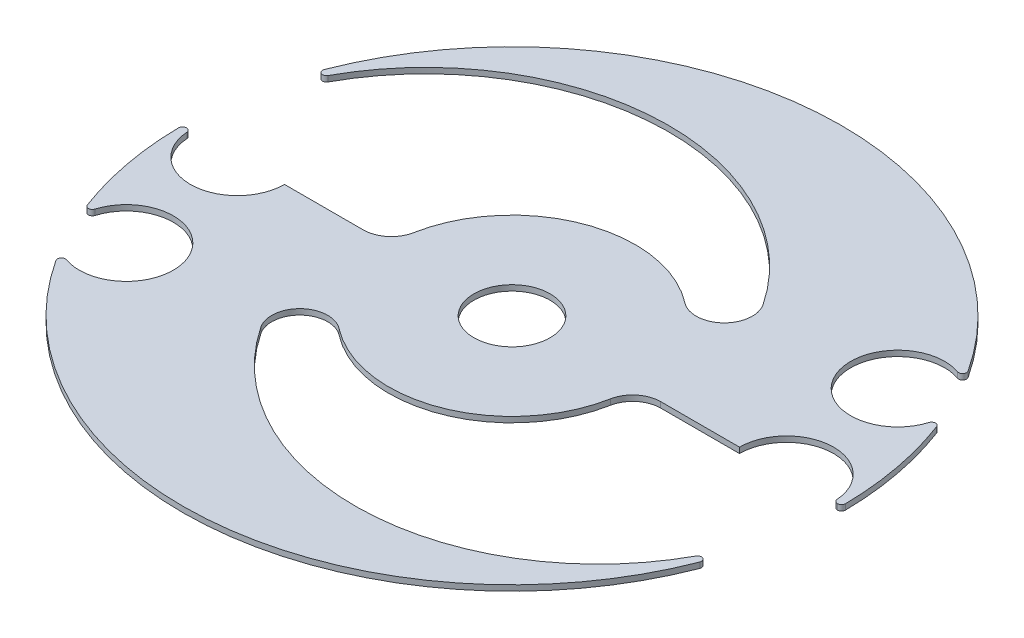
SolidWorks part; units mm, degrees
ref_plane "Front Plane" through (0, 0, 0) normal (0, 0, 1) x (1, 0, 0)
ref_plane "Top Plane" through (0, 0, 0) normal (0, 1, 0) x (1, 0, 0)
ref_plane "Right Plane" through (0, 0, 0) normal (1, 0, 0) x (0, 0, -1)
sketch "Sketch1" plane through (0, 0, 0) normal (0, 1, 0) x (1, 0, 0)
  line L0 (-66.1373, -33.5533) -> (66.1373, 33.5533) construction
  line L1 (-75.4788, 0) -> (75.4788, 0) construction
  line L2 (0, -72.0468) -> (0, 72.0468) construction
  line L3 (15.4, -72.0468) -> (15.4, 72.0468) construction
  line L4 (-15.4, -72.0468) -> (-15.4, 72.0468) construction
  line L5 (-58.0958, 0) -> (-58.073, 0)
  line L6 (58.073, 0) -> (58.0958, 0)
  line L7 (40.6, 0) -> (26.533, 0)
  line L9 (-40.6, 0) -> (-26.533, 0)
  arc A0 (58.7957, 0.7084) -> (55.017, 20.75) centre (0, 0) ccw
  circle A1 centre (0, 0) radius 14
  arc A2 (13.4497, 17.4099) -> (-21.6195, 4.0741) centre (0, 0) ccw
  circle A3 centre (0, 0) radius 51.2 construction
  arc A5 (48.4216, 31.0978) -> (53.6927, 20.7078) centre (45.66, 23.1647) ccw
  arc A6 (-48.4216, -31.0978) -> (-53.6927, -20.7078) centre (-45.66, -23.1647) ccw
  arc A7 (-58.7957, -0.7084) -> (-55.017, -20.75) centre (0, 0) ccw
  arc A8 (-57.3751, -0.6462) -> (-40.6, 0) centre (-49, 0) ccw
  arc A9 (40.6, 0) -> (57.3751, 0.6462) centre (49, 0) cw
  arc A10 (49.2378, 32.1415) -> (48.4216, 31.0978) centre (48.6517, 31.7588) cw
  arc A11 (55.017, 20.75) -> (53.6927, 20.7078) centre (54.3621, 20.503) ccw
  arc A12 (-48.4216, -31.0978) -> (-49.2378, -32.1415) centre (-48.6517, -31.7588) ccw
  arc A13 (-53.6927, -20.7078) -> (-55.017, -20.75) centre (-54.3621, -20.503) cw
  arc A15 (-58.073, 0) -> (-57.3751, -0.6462) centre (-58.073, -0.7) cw
  arc A16 (20.661, 24.1488) -> (-53.5394, 20.711) centre (-15.4, 0) ccw
  arc A17 (-58.0958, 0) -> (-58.7957, -0.7084) centre (-58.0958, -0.7) ccw
  arc A18 (49.2378, 32.1415) -> (-54.807, 21.2986) centre (0, 0) ccw
  arc A19 (-53.5394, 20.711) -> (-54.807, 21.2986) centre (-54.1545, 21.0451) cw
  arc A20 (-20.661, -24.1488) -> (53.5394, -20.711) centre (15.4, 0) ccw
  arc A21 (58.073, 0) -> (57.3751, 0.6462) centre (58.073, 0.7) cw
  arc A22 (58.0958, 0) -> (58.7957, 0.7084) centre (58.0958, 0.7) ccw
  arc A23 (13.4497, 17.4099) -> (20.661, 24.1488) centre (16.5065, 21.3667) ccw
  arc A24 (26.533, 0) -> (21.6195, -4.0741) centre (26.533, -5) ccw
  arc A25 (-49.2378, -32.1415) -> (54.807, -21.2986) centre (0, 0) ccw
  arc A26 (54.807, -21.2986) -> (53.5394, -20.711) centre (54.1545, -21.0451) ccw
  arc A27 (-21.6195, 4.0741) -> (-26.533, 0) centre (-26.533, 5) cw
  arc A28 (21.6195, -4.0741) -> (-13.4497, -17.4099) centre (0, 0) cw
  arc A29 (-20.661, -24.1488) -> (-13.4497, -17.4099) centre (-16.5065, -21.3667) cw
  point P8 (0, 0)
  point P11 (0, 0)
  point P24 (0, 0)
  point P46 (-58.0844, 0)
  dimension "D1" = 117.6
  dimension "D2" = 44
  dimension "D3" = 28
  dimension "D5" = 102.4
  dimension "D6" = 16.8
  dimension "D7" = 16.8
  dimension "D9" = 16.8
  dimension "D10" = 0.7
  dimension "D11" = 0.7
  dimension "D12" = 15.4
  dimension "D13" = 43.4
  dimension "D14" = 0.7
  dimension "D15" = 58.8
  dimension "D16" = 0.7
  dimension "D17" = 86.8
  dimension "D18" = 0.7
  dimension "D19" = 0.7
  dimension "D20" = 5
  dimension "D21" = 5
  dimension "D22" = 58.8
  dimension "D23" = 0.7
  dimension "D24" = 5
  dimension "D25" = 22
  dimension "D26" = 5
  dimension "D4" = 26.9
  dimension "D8" = 49
extrude "Boss-Extrude1" add sketch "Sketch1" along normal blind 1 contours A2 A27 L9 A8 A15 L5 A17 A7 A13 A6 A12 A25 A26 A20 A29 A28 A24 L7 A9 A21 L6 A22 A0 A11 A5 A10 A18 A19 A16 A23
sketch "Sketch3" plane through (0, 1, 0) normal (0, 1, 0) x (1, 0, 0)
  circle A0 centre (0, 0) radius 6.8
  dimension "D1" = 13.6
extrude "Cut-Extrude1" cut sketch "Sketch3" against normal blind 10 contours A0
